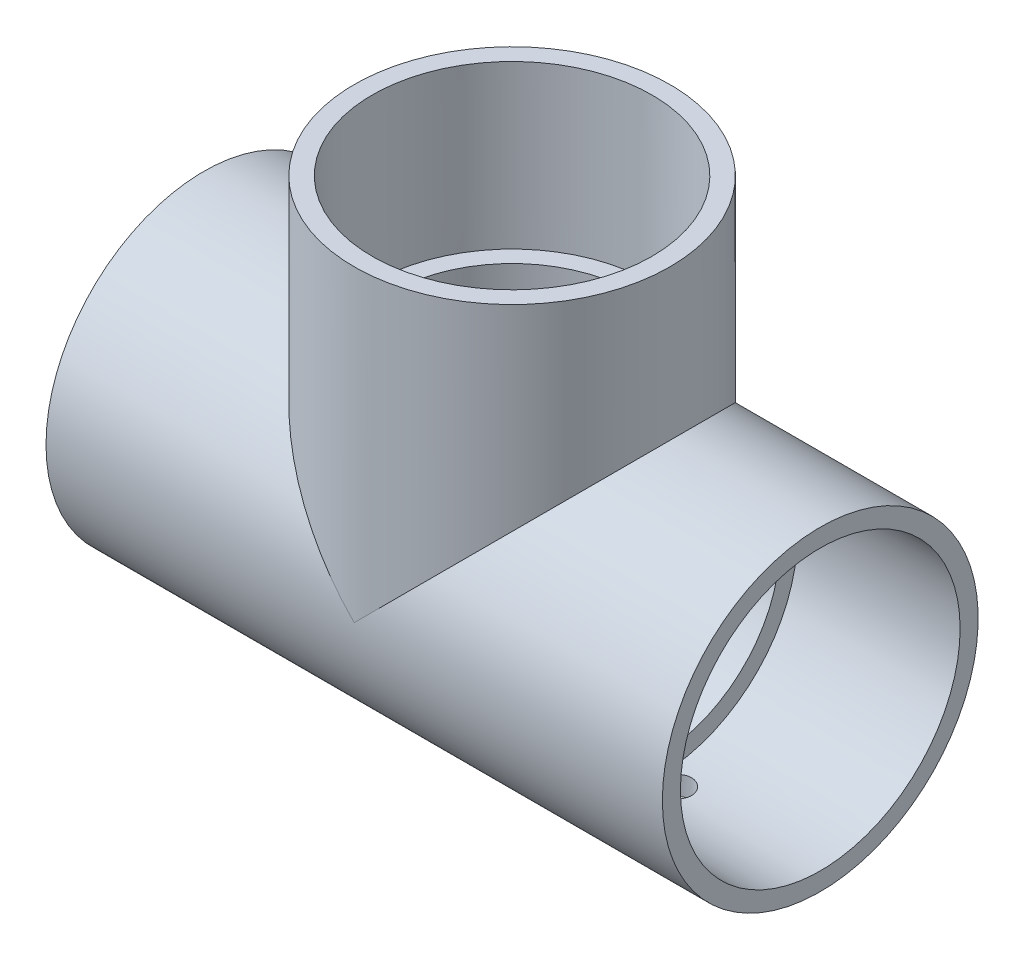
SolidWorks part; units mm, degrees
ref_plane "Front Plane" through (0, 0, 0) normal (0, 0, 1) x (1, 0, 0)
ref_plane "Top Plane" through (0, 0, 0) normal (0, 1, 0) x (1, 0, 0)
ref_plane "Right Plane" through (0, 0, 0) normal (1, 0, 0) x (0, 0, -1)
sketch "Sketch0" plane through (0, 0, 0) normal (0, 0, 1) x (1, 0, 0)
  line L0 (-66.802, 0) -> (0, 0) construction
  line L1 (0, 0) -> (0, 66.802) construction
  line L2 (-31.75, 0) -> (0, 0) construction
  line L3 (0, 0) -> (0, 31.75) construction
  line L4 (-66.802, 34.2265) -> (-66.802, -34.2265) construction
  line L5 (-31.75, 30.0863) -> (-66.802, 30.3149) construction
  line L6 (-31.75, 30.0863) -> (-31.75, -30.0863) construction
  line L7 (-31.75, -30.0863) -> (-66.802, -30.3149) construction
  line L8 (-66.802, 30.3149) -> (-66.802, -30.3149) construction
  line L9 (-34.2265, 66.802) -> (34.2265, 66.802) construction
  line L10 (-30.3149, 66.802) -> (30.3149, 66.802) construction
  line L11 (30.3149, 66.802) -> (30.0863, 31.75) construction
  line L12 (30.0863, 31.75) -> (-30.0863, 31.75) construction
  line L13 (-30.0863, 31.75) -> (-30.3149, 66.802) construction
  line L14 (-31.75, 26.2509) -> (-31.75, -26.2509) construction
  line L15 (-66.802, 0) -> (-31.75, 0) construction
  line L16 (0, 66.802) -> (0, 31.75) construction
  line L17 (0, 0) -> (31.75, 0) construction
  line L18 (-26.2509, 31.75) -> (26.2509, 31.75) construction
  line L19 (31.75, 0) -> (66.802, 0) construction
  dimension "H" = 66.802
  dimension "G" = 31.75
  dimension "M" = 68.453
  dimension "OD A" = 60.6298
  dimension "OD B" = 60.1726
  dimension "ID" = 52.5018
  dimension "H3" = 66.802
sketch "Sketch1" plane through (0, 0, 0) normal (0, 0, 1) x (1, 0, 0)
  line L0 (-66.802, 0) -> (0, 0) construction
  line L1 (-66.802, 0) -> (0, 0) construction
  line L2 (0, 0) -> (0, -34.2265) construction
  line L3 (-66.802, -34.2265) -> (-31.75, -34.2265)
  line L4 (-66.802, -34.2265) -> (-66.802, -30.3149)
  line L5 (-66.802, -30.3149) -> (-31.75, -30.0863)
  line L6 (-31.75, -34.2265) -> (-31.75, -30.0863)
  line L7 (-31.75, -34.2265) -> (0, -34.2265) construction
  line L8 (66.802, -30.3149) -> (31.75, -30.0863)
  line L9 (66.802, -34.2265) -> (66.802, -30.3149)
  line L10 (31.75, -34.2265) -> (31.75, -30.0863)
  line L11 (66.802, -34.2265) -> (31.75, -34.2265)
revolve "Revolve1" add sketch "Sketch1" angle 360 about L1
sketch "Sketch2" plane through (0, 0, 0) normal (0, 0, 1) x (1, 0, 0)
  line L0 (30.3149, 66.802) -> (30.0863, 31.75)
  line L1 (30.0863, 31.75) -> (34.2265, 31.75)
  line L2 (34.2265, 31.75) -> (34.2265, 66.802)
  line L3 (34.2265, 66.802) -> (30.3149, 66.802)
  line L4 (0, 0) -> (0, 66.802) construction
  line L5 (0, 0) -> (0, 66.802) construction
revolve "Revolve2" add sketch "Sketch2" angle 360 about L5
sketch "Sketch3" plane through (-31.75, 0, 0) normal (1, 0, 0) x (0, 0, -1)
  circle A0 centre (0, 0) radius 26.2509
  circle A1 centre (0, 0) radius 34.2265
sketch "Sketch4" plane through (-31.75, 0, 0) normal (1, 0, 0) x (0, 0, -1)
  circle A0 centre (0, 0) radius 34.2265 construction
  circle A1 centre (0, 0) radius 34.2265
extrude "Boss-Extrude1" add sketch "Sketch4" along normal up to vertex
sketch "Sketch5" plane through (0, 31.75, 0) normal (0, -1, 0) x (1, 0, 0)
  circle A0 centre (0, 0) radius 34.2265 construction
  circle A1 centre (0, 0) radius 34.2265
extrude "Boss-Extrude2" add sketch "Sketch5" along normal up to vertex (31.75 mm away) up to point (0, 0, 0)
sketch "Sketch6" plane through (0, 0, 0) normal (0, 0, 1) x (1, 0, 0)
  line L0 (-66.802, -30.3149) -> (-31.75, -30.0863)
  line L1 (-31.75, -30.0863) -> (-31.75, -26.2509)
  line L2 (-31.75, -26.2509) -> (31.75, -26.2509)
  line L3 (31.75, -30.0863) -> (31.75, 27.2359) construction
  line L4 (0, -26.2509) -> (0, 0) construction
  line L5 (31.75, -30.0863) -> (31.75, -26.2509)
  line L6 (66.802, -30.3149) -> (66.802, 30.3149) construction
  line L7 (66.802, -34.2265) -> (66.802, 34.2265) construction
  line L8 (66.802, -30.3149) -> (66.802, 0)
  line L9 (66.802, 0) -> (-66.802, 0)
  line L10 (-66.802, 0) -> (-66.802, -30.3149)
  line L11 (66.802, -30.3149) -> (31.75, -30.0863)
revolve "Cut-Revolve1" cut sketch "Sketch6" angle 360 about L9
sketch "Sketch7" plane through (0, 0, 0) normal (0, 0, 1) x (1, 0, 0)
  line L0 (30.3149, 66.802) -> (30.0863, 31.75)
  line L1 (30.0863, 31.75) -> (26.2509, 31.75)
  line L2 (26.2509, 31.75) -> (26.2509, 0)
  line L3 (0, 0) -> (31.75, 0) construction
  line L4 (26.2509, 0) -> (0, 0)
  line L5 (0, 0) -> (0, 66.802)
  line L6 (-34.2265, 66.802) -> (34.2265, 66.802) construction
  line L7 (0, 66.802) -> (30.3149, 66.802)
revolve "Cut-Revolve2" cut sketch "Sketch7" angle 360 about L5
sketch "Sketch8" plane through (0, 0, 0) normal (0, 1, 0) x (1, 0, 0)
  circle A0 centre (35.7188, 0) radius 3.175
  circle A1 centre (-35.7188, 0) radius 3.175
  dimension "D1" = 6.35
  dimension "D2" = 6.35
  dimension "D3" = 35.7188
  dimension "D4" = 71.4375
extrude "Cut-Extrude1" cut sketch "Sketch8" against normal up to next
